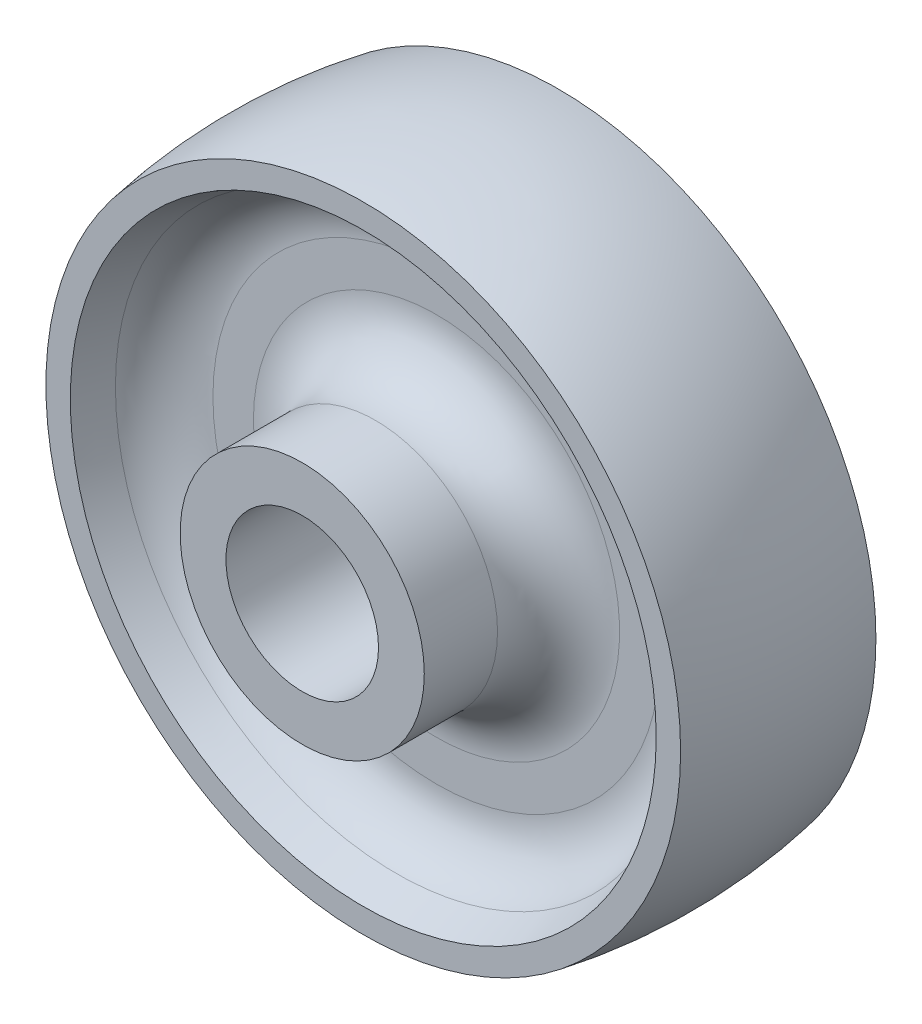
SolidWorks part; units mm, degrees
ref_plane "Piano frontale" through (0, 0, 0) normal (0, 0, 1) x (1, 0, 0)
ref_plane "Piano superiore" through (0, 0, 0) normal (0, 1, 0) x (1, 0, 0)
ref_plane "Piano destro" through (0, 0, 0) normal (1, 0, 0) x (0, 0, -1)
sketch "Schizzo1" plane through (0, 0, 0) normal (1, 0, 0) x (0, 0, -1)
  line L0 (0, 0) -> (99.477, 0) construction
  line L1 (0, 0) -> (0, 58.5719) construction
  line L2 (26, 12.5) -> (-26, 12.5)
  line L3 (-26, 12.5) -> (-26, 20)
  line L4 (-26, 20) -> (-4, 20)
  line L5 (-4, 20) -> (-4, 43.6324)
  line L6 (-4, 43.6324) -> (-16, 48)
  line L7 (-16, 48) -> (-16, 52)
  line L8 (-16, 52) -> (16, 52) construction
  line L9 (16, 52) -> (16, 48)
  line L10 (16, 48) -> (4, 43.6324)
  line L11 (4, 43.6324) -> (4, 20)
  line L12 (4, 20) -> (26, 20)
  line L13 (26, 20) -> (26, 12.5)
  arc A0 (-16, 52) -> (16, 52) centre (0, -36.5664) cw
  dimension "D12" = 90
  dimension "D1" = 25
  dimension "D2" = 26
  dimension "D3" = 52
  dimension "D4" = 40
  dimension "D5" = 4
  dimension "D6" = 8
  dimension "D7" = 16
  dimension "D8" = 32
  dimension "D9" = 96
  dimension "D10" = 4
  dimension "D11" = 20
revolve "Rivoluzione1" add sketch "Schizzo1" angle 360 about L0
fillet "Raccordo1" radius 10 2 edges at (43.6324, 0, -4) (20, 0, -4)
fillet "Raccordo2" radius 10 2 edges at (43.6324, 0, 4) (20, 0, 4)
